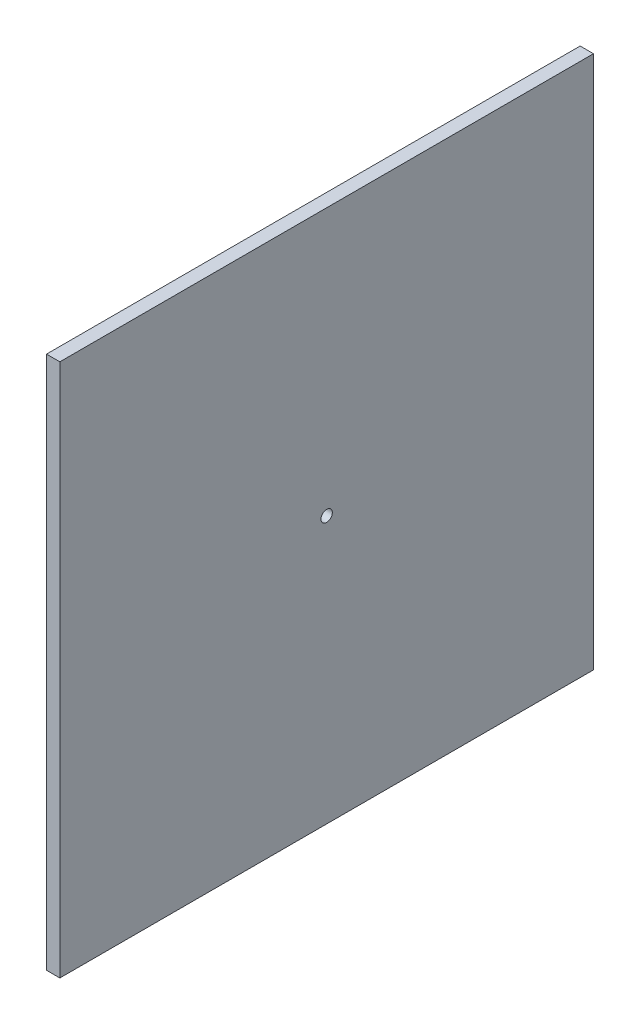
SolidWorks part; units mm, degrees
ref_plane "Front Plane" through (0, 0, 0) normal (0, 0, 1) x (1, 0, 0)
ref_plane "Top Plane" through (0, 0, 0) normal (0, 1, 0) x (1, 0, 0)
ref_plane "Right Plane" through (0, 0, 0) normal (1, 0, 0) x (0, 0, -1)
sketch "Sketch1" plane through (0, 0, 0) normal (1, 0, 0) x (0, 0, -1)
  line L1 (-200, -200) -> (200, -200)
  line L2 (-200, -200) -> (-200, 200)
  line L3 (-200, 200) -> (200, 200)
  line L4 (200, -200) -> (200, 200)
  line L5 (-200, -200) -> (200, 200) construction
  line L6 (-200, 200) -> (200, -200) construction
  circle A0 centre (0, 0) radius 4.25
  point P0 (0, 0)
  dimension "D3" = 8.5
  dimension "D1" = 400
  dimension "D2" = 400
extrude "Boss-Extrude1" add sketch "Sketch1" along normal blind 10
